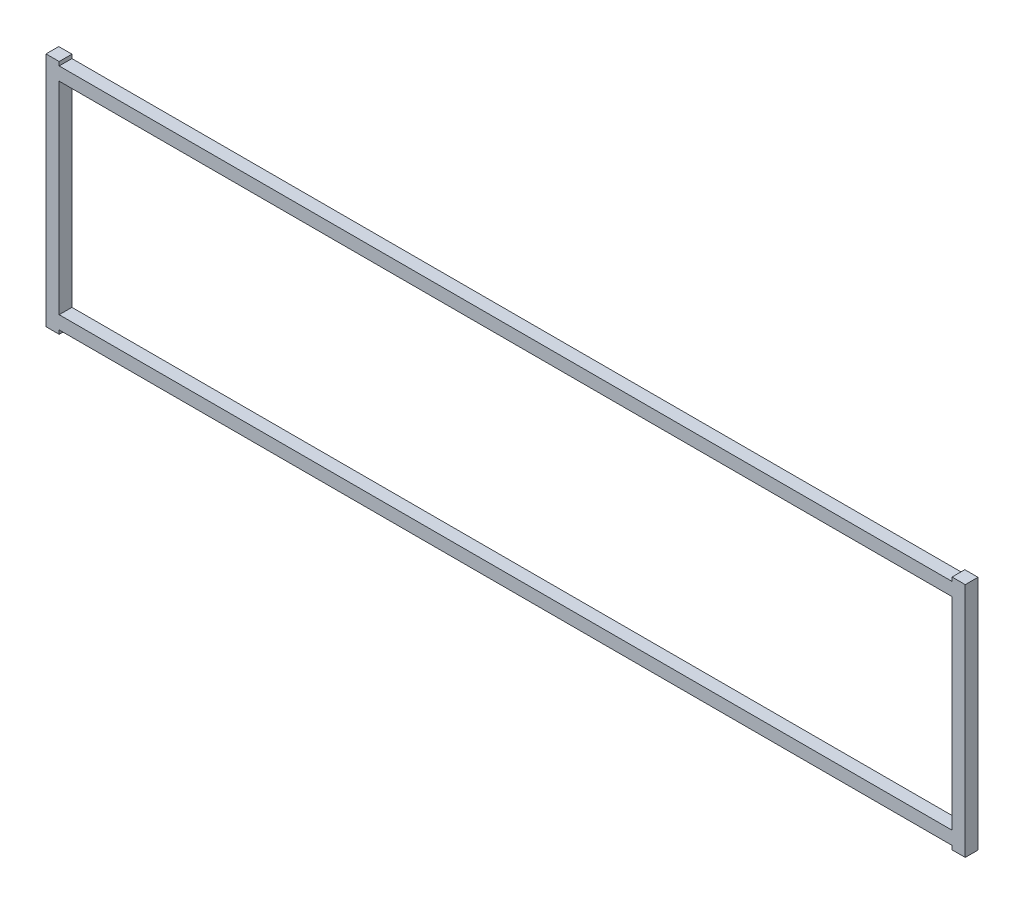
SolidWorks part; units mm, degrees
ref_plane "Front" through (0, 0, 0) normal (0, 0, 1) x (1, 0, 0)
ref_plane "Top" through (0, 0, 0) normal (0, 1, 0) x (1, 0, 0)
ref_plane "Right" through (0, 0, 0) normal (1, 0, 0) x (0, 0, -1)
sketch "Sketch1" plane through (0, 0, 0) normal (0, 0, 1) x (1, 0, 0)
  line L0 (222.1484, -58.7851) -> (228.7016, -58.7851)
  line L1 (228.7016, -58.7851) -> (228.7016, 58.7851)
  line L2 (228.7016, 58.7851) -> (222.1484, 58.7851)
  line L3 (222.1484, 58.7851) -> (222.1484, 56.8769)
  line L4 (222.1484, 56.8769) -> (-222.1484, 56.8769)
  line L5 (-222.1484, 56.8769) -> (-222.1484, 58.7851)
  line L6 (-222.1484, 58.7851) -> (-228.7016, 58.7851)
  line L7 (-228.7016, 58.7851) -> (-228.7016, -58.7851)
  line L8 (-228.7016, -58.7851) -> (-222.1484, -58.7851)
  line L9 (-222.1484, -58.7851) -> (-222.1484, -56.877)
  line L10 (-222.1484, -56.877) -> (222.1484, -56.877)
  line L11 (222.1484, -56.877) -> (222.1484, -58.7851)
  line L12 (222.1484, -50.3237) -> (222.1484, 50.3237)
  line L13 (-222.1484, -50.3237) -> (222.1484, -50.3237)
  line L14 (-222.1484, 50.3237) -> (-222.1484, -50.3237)
  line L15 (222.1484, 50.3237) -> (-222.1484, 50.3237)
extrude "Boss-Extrude1" add sketch "Sketch1" along normal blind 6.35
